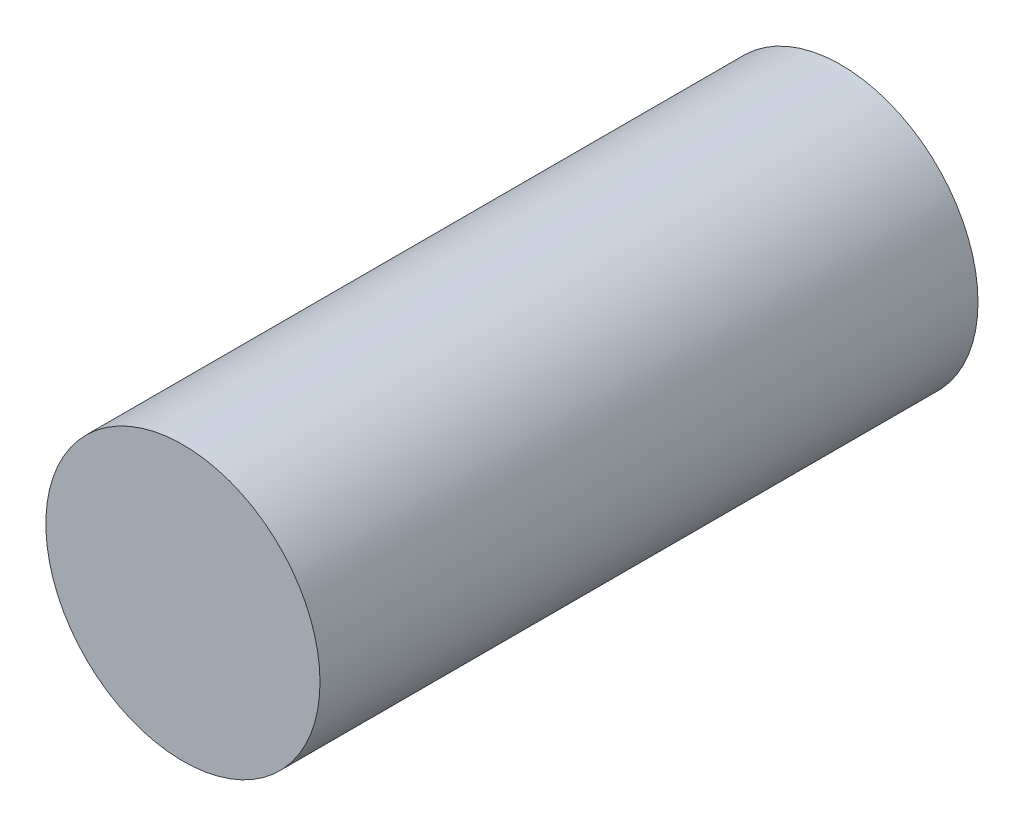
SolidWorks part; units mm, degrees
ref_plane "Front Plane" through (0, 0, 0) normal (0, 0, 1) x (1, 0, 0)
ref_plane "Top Plane" through (0, 0, 0) normal (0, 1, 0) x (1, 0, 0)
ref_plane "Right Plane" through (0, 0, 0) normal (1, 0, 0) x (0, 0, -1)
sketch "Sketch1" plane through (0, 0, 0) normal (0, 0, 1) x (1, 0, 0)
  circle A0 centre (0, 0) radius 12.5
  dimension "D1" = 25
extrude "Boss-Extrude1" add sketch "Sketch1" along normal blind 60
